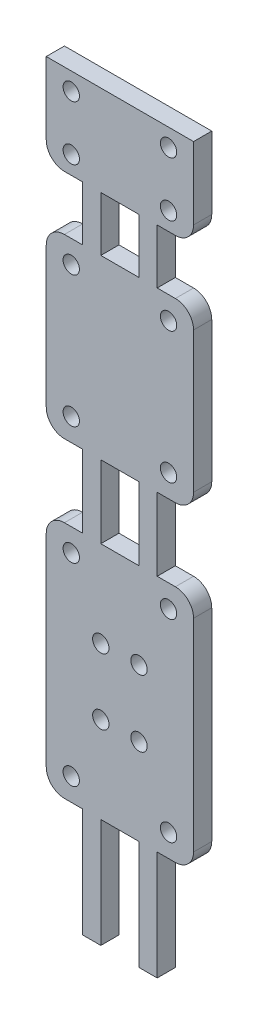
SolidWorks part; units mm, degrees
ref_plane "Front Plane" through (0, 0, 0) normal (0, 0, 1) x (1, 0, 0)
ref_plane "Top Plane" through (0, 0, 0) normal (0, 1, 0) x (1, 0, 0)
ref_plane "Right Plane" through (0, 0, 0) normal (1, 0, 0) x (0, 0, -1)
sketch "Sketch3" plane through (0, 0, 0) normal (0, 0, 1) x (1, 0, 0)
  line L0 (0, 94.0064) -> (0, 86.0614)
  line L1 (16.2, 94.0064) -> (16.2, 86.0614)
  line L2 (0, -0.1536) -> (16.2, -0.1536) construction
  line L3 (0, 76.0614) -> (0, 60.6064)
  line L4 (0, 94.0064) -> (16.2, 94.0064)
  line L5 (0, 12.3464) -> (4, 12.3464) construction
  line L6 (2, 58.6064) -> (4, 58.6064)
  line L7 (16.2, 76.0614) -> (16.2, 60.6064)
  line L8 (0, 48.6064) -> (0, 26.3464)
  line L9 (16.2, 48.6064) -> (16.2, 26.3464)
  line L10 (16.2, 12.3464) -> (16.2, -0.1536) construction
  line L11 (0, 12.3464) -> (0, -0.1536) construction
  line L12 (6, 12.3464) -> (6, 24.3464)
  line L13 (6, 24.3464) -> (10.2, 24.3464)
  line L14 (4, 12.3464) -> (4, 24.3464)
  line L15 (6, 12.3464) -> (10.2, 12.3464) construction
  line L16 (4, 50.6064) -> (4, 58.6064)
  line L17 (4, 78.0614) -> (4, 84.0614)
  line L18 (6, 50.6064) -> (6, 58.6064)
  line L19 (6, 78.0614) -> (6, 84.0614)
  line L20 (6, 84.0614) -> (10.2, 84.0614)
  line L21 (6, 78.0614) -> (10.2, 78.0614)
  line L22 (6, 58.6064) -> (10.2, 58.6064)
  line L23 (6, 50.6064) -> (10.2, 50.6064)
  line L24 (8.1, 94.0064) -> (8.1, -0.1536) construction
  line L25 (12.2, 50.6064) -> (12.2, 58.6064)
  line L26 (2, 50.6064) -> (4, 50.6064)
  line L27 (2, 24.3464) -> (4, 24.3464)
  line L28 (10.2, 12.3464) -> (10.2, 24.3464)
  line L29 (12.2, 12.3464) -> (12.2, 24.3464)
  line L30 (2, 78.0614) -> (4, 78.0614)
  line L31 (10.2, 50.6064) -> (10.2, 58.6064)
  line L32 (2, 84.0614) -> (4, 84.0614)
  line L33 (12.2, 78.0614) -> (12.2, 84.0614)
  line L34 (10.2, 78.0614) -> (10.2, 84.0614)
  line L35 (12.2, 84.0614) -> (14.2, 84.0614)
  line L36 (12.2, 78.0614) -> (14.2, 78.0614)
  line L37 (12.2, 58.6064) -> (14.2, 58.6064)
  line L38 (12.2, 50.6064) -> (14.2, 50.6064)
  line L39 (12.2, 12.3464) -> (16.2, 12.3464) construction
  line L40 (12.2, 24.3464) -> (14.2, 24.3464)
  line L41 (4, 12.3464) -> (6, 12.3464)
  line L42 (10.2, 12.3464) -> (12.2, 12.3464)
  circle A0 centre (6, 33.8464) radius 0.9
  circle A1 centre (10.2, 33.8464) radius 0.9
  circle A2 centre (2.75, 86.0614) radius 0.9
  circle A3 centre (10.2, 41.1664) radius 0.9
  circle A4 centre (13.45, 48.1064) radius 0.9
  circle A5 centre (2.75, 92.0614) radius 0.9
  circle A6 centre (13.45, 86.0614) radius 0.9
  circle A7 centre (2.75, 61.1064) radius 0.9
  arc A8 (14.2, 24.3464) -> (16.2, 26.3464) centre (14.2, 26.3464) ccw
  arc A9 (16.2, 48.6064) -> (14.2, 50.6064) centre (14.2, 48.6064) ccw
  arc A10 (2, 50.6064) -> (0, 48.6064) centre (2, 48.6064) ccw
  arc A11 (0, 26.3464) -> (2, 24.3464) centre (2, 26.3464) ccw
  arc A12 (0, 60.6064) -> (2, 58.6064) centre (2, 60.6064) ccw
  arc A13 (14.2, 58.6064) -> (16.2, 60.6064) centre (14.2, 60.6064) ccw
  arc A14 (16.2, 76.0614) -> (14.2, 78.0614) centre (14.2, 76.0614) ccw
  arc A15 (0, 76.0614) -> (2, 78.0614) centre (2, 76.0614) cw
  circle A16 centre (2.85, 9.8464) radius 0.9 construction
  circle A17 centre (13.35, 9.8464) radius 0.9 construction
  circle A18 centre (13.35, 3.8464) radius 0.9 construction
  circle A19 centre (2.85, 3.8464) radius 0.9 construction
  circle A20 centre (13.45, 61.1064) radius 0.9
  circle A21 centre (2.75, 75.5614) radius 0.9
  circle A22 centre (13.45, 26.8464) radius 0.9
  circle A23 centre (13.45, 75.5614) radius 0.9
  circle A24 centre (13.45, 92.0614) radius 0.9
  circle A25 centre (2.75, 26.8464) radius 0.9
  circle A26 centre (6, 41.1064) radius 0.9
  circle A27 centre (2.75, 48.1064) radius 0.9
  arc A28 (16.2, 86.0614) -> (14.2, 84.0614) centre (14.2, 86.0614) cw
  arc A29 (2, 84.0614) -> (0, 86.0614) centre (2, 86.0614) cw
  point P76 (16.2, 24.3464)
  point P80 (16.2, 50.6064)
  point P84 (0, 50.6064)
  point P88 (0, 24.3464)
  point P95 (0, 58.6064)
  point P99 (16.2, 58.6064)
  point P102 (16.2, 78.0614)
  point P105 (0, 78.0614)
  point P108 (16.2, 84.0614)
  point P111 (0, 84.0614)
  dimension "D1" = 2.5
  dimension "D2" = 9.5
  dimension "D32" = 6
  dimension "D33" = 6
  dimension "D49" = 1.8
  dimension "D50" = 2
  dimension "D3" = 2.5
  dimension "D4" = 9.5
  dimension "D5" = 6
  dimension "D6" = 2.75
  dimension "D7" = 2.75
  dimension "D8" = 6
  dimension "D9" = 2.5
  dimension "D10" = 2.5
  dimension "D11" = 9.5
  dimension "D12" = 9.44
  dimension "D13" = 2.75
  dimension "D14" = 6
  dimension "D15" = 2.75
  dimension "D16" = 6
  dimension "D17" = 12
  dimension "D18" = 2.5
  dimension "D19" = 4
  dimension "D20" = 6
  dimension "D21" = 6
  dimension "D22" = 4
  dimension "D23" = 2.85
  dimension "D24" = 2.85
  dimension "D25" = 26.26
  dimension "D26" = 16.2
  dimension "D27" = 8
  dimension "D28" = 2.5
  dimension "D29" = 2.5
  dimension "D30" = 2.75
  dimension "D31" = 2.75
  dimension "D34" = 2.5
  dimension "D35" = 2.5
  dimension "D36" = 2.75
  dimension "D37" = 2.75
  dimension "D38" = 19.455
  dimension "D39" = 6
  dimension "D40" = 2
  dimension "D41" = 2
  dimension "D42" = 2.75
  dimension "D43" = 2.75
  dimension "D44" = 2.5
  dimension "D45" = 4
  dimension "D46" = 2.75
  dimension "D47" = 2.75
  dimension "D48" = 9.945
extrude "Boss-Extrude3" add sketch "Sketch3" along normal blind 2
sketch "Sketch4" plane through (0, 0, 2) normal (0, 0, 1) x (1, 0, 0)
  line L0 (4, 84.0614) -> (12.2, 84.0614)
  line L1 (12.2, 84.0614) -> (12.2, 78.0614)
  line L2 (12.2, 78.0614) -> (4, 78.0614)
  line L3 (4, 78.0614) -> (4, 84.0614)
  line L4 (4, 58.6064) -> (12.2, 58.6064)
  line L5 (12.2, 58.6064) -> (12.2, 50.6064)
  line L6 (12.2, 50.6064) -> (4, 50.6064)
  line L7 (4, 50.6064) -> (4, 58.6064)
  line L8 (4, 24.3464) -> (12.2, 24.3464)
  line L9 (12.2, 24.3464) -> (12.2, 12.3464)
  line L10 (12.2, 12.3464) -> (4, 12.3464)
  line L11 (4, 12.3464) -> (4, 24.3464)
extrude "Cut-Extrude1" [suppressed] cut sketch "Sketch4" against normal up to surface (2 mm away)
equation "\"D25@Sketch3\"= \"HL@parametersSketch@prostheticParameters.SLDPRT\" * 0.196 - 4 - 6'Index PIP length"
equation "\"D26@Sketch3\"= \"fingerWidth@parametersSketch@prostheticParameters.SLDPRT\"'Index Width"
equation "\"D38@Sketch3\"= \"HL@parametersSketch@prostheticParameters.SLDPRT\" * 0.143 - 3 - 4 'Index MIP Length"
equation "\"D48@Sketch3\"= \"HL@parametersSketch@prostheticParameters.SLDPRT\" * 0.097 - 3 - 5'Index DIP Length - Gap Fingertip"
equation "\"D49@Sketch3\"= 1.5 + \"tol1@parametersSketch@prostheticParameters.SLDPRT\""
